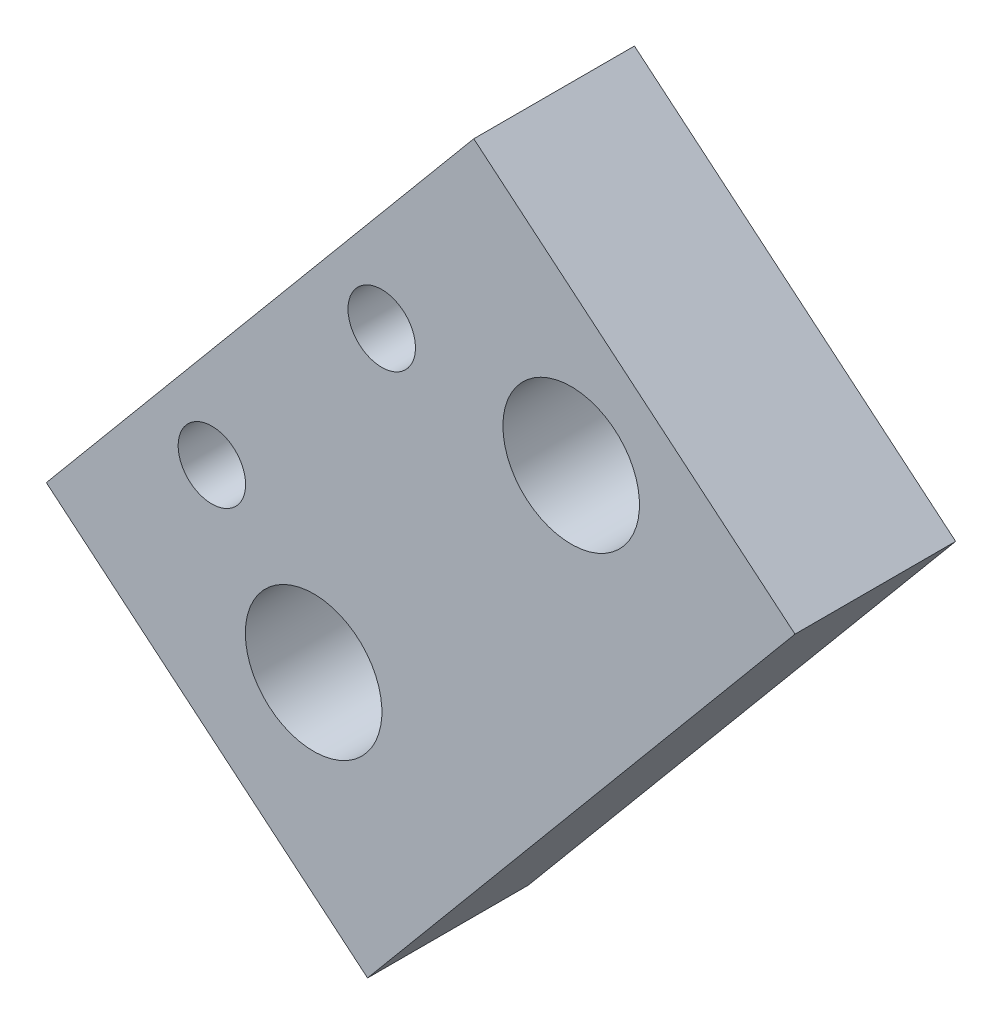
SolidWorks part; units mm, degrees
ref_plane "Front Plane" through (0, 0, 0) normal (0, 0, 1) x (1, 0, 0)
ref_plane "Top Plane" through (0, 0, 0) normal (0, 1, 0) x (1, 0, 0)
ref_plane "Right Plane" through (0, 0, 0) normal (1, 0, 0) x (0, 0, -1)
sketch "Sketch2" plane through (0, 0, 32430.9661) normal (0, 0, -1) x (-1, 0, 0)
  line L0 (-107.2871, 528.6308) -> (-87.2957, 545.3368)
  line L1 (-107.2871, 528.6308) -> (-80.6838, 496.7956)
  line L2 (-87.2957, 545.3368) -> (-60.6923, 513.5017)
  line L3 (-80.6838, 496.7956) -> (-60.6923, 513.5017)
  circle A0 centre (-77.327, 511.5826) radius 4.25
  circle A1 centre (-93.3579, 530.7661) radius 4.25
  circle A3 centre (-81.5669, 532.2512) radius 2.1
  circle A4 centre (-70.9945, 519.5996) radius 2.1
  circle A8 centre (79.8447, 514.5954) radius 11 construction
  dimension "D3" = 8.5
  dimension "D4" = 8.5
  dimension "D5" = 3.9951
  dimension "D1" = 7.2934
  dimension "D2" = 11.2854
  dimension "D6" = 13.7146
  dimension "D7" = 9.1942
  dimension "D8" = 3.9951
  dimension "D9" = 12.0578
  dimension "D10" = 12.0578
extrude "Boss-Extrude1" add sketch "Sketch2" along normal blind 10
